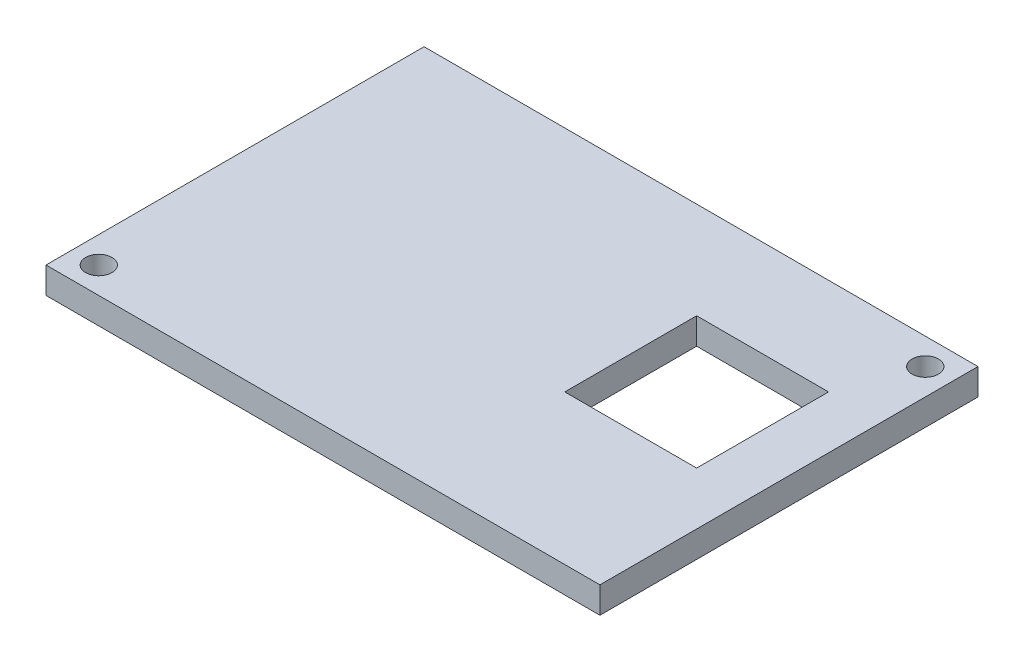
SolidWorks part; units mm, degrees
ref_plane "Front Plane" through (0, 0, 0) normal (0, 0, 1) x (1, 0, 0)
ref_plane "Top Plane" through (0, 0, 0) normal (0, 1, 0) x (1, 0, 0)
ref_plane "Right Plane" through (0, 0, 0) normal (1, 0, 0) x (0, 0, -1)
sketch "Sketch2" plane through (0, 0, 0) normal (0, 1, 0) x (1, 0, 0)
  line L1 (-31.8844, 22.6701) -> (31.1156, 22.6701)
  line L2 (-31.8844, 22.6701) -> (-31.8844, -20.3299)
  line L3 (-31.8844, -20.3299) -> (31.1156, -20.3299)
  line L4 (31.1156, 22.6701) -> (31.1156, -20.3299)
  dimension "D1" = 43
  dimension "D2" = 63
extrude "Boss-Extrude1" add sketch "Sketch2" along normal blind 3
sketch "Sketch3" plane through (0, 3, 0) normal (0, 1, 0) x (1, 0, 0)
  line L0 (31.1156, 22.6701) -> (-31.8844, 22.6701) construction
  line L1 (31.1156, -20.3299) -> (31.1156, 22.6701) construction
  circle A0 centre (28.1156, 19.6701) radius 1.5
  dimension "D1" = 3
  dimension "D2" = 3
extrude "Cut-Extrude1" cut sketch "Sketch3" against normal blind 3
sketch "Sketch4" plane through (0, 3, 0) normal (0, 1, 0) x (1, 0, 0)
  line L0 (-31.8844, 22.6701) -> (-31.8844, -20.3299) construction
  line L1 (-31.8844, -20.3299) -> (31.1156, -20.3299) construction
  circle A0 centre (-28.8844, -17.3299) radius 1.5
  dimension "D1" = 3
  dimension "D2" = 3
extrude "Cut-Extrude2" cut sketch "Sketch4" against normal blind 3
sketch "Sketch5" plane through (0, 3, 0) normal (0, 1, 0) x (1, 0, 0)
  line L0 (-31.8844, -20.3299) -> (31.1156, -20.3299) construction
  line L1 (10.1156, 11.6701) -> (25.1156, 11.6701)
  line L2 (10.1156, 11.6701) -> (10.1156, -3.3299)
  line L3 (10.1156, -3.3299) -> (25.1156, -3.3299)
  line L4 (25.1156, 11.6701) -> (25.1156, -3.3299)
  line L5 (31.1156, -20.3299) -> (31.1156, 22.6701) construction
  dimension "D1" = 15
  dimension "D2" = 15
  dimension "D3" = 17
  dimension "D4" = 6
extrude "Cut-Extrude3" cut sketch "Sketch5" against normal blind 3
